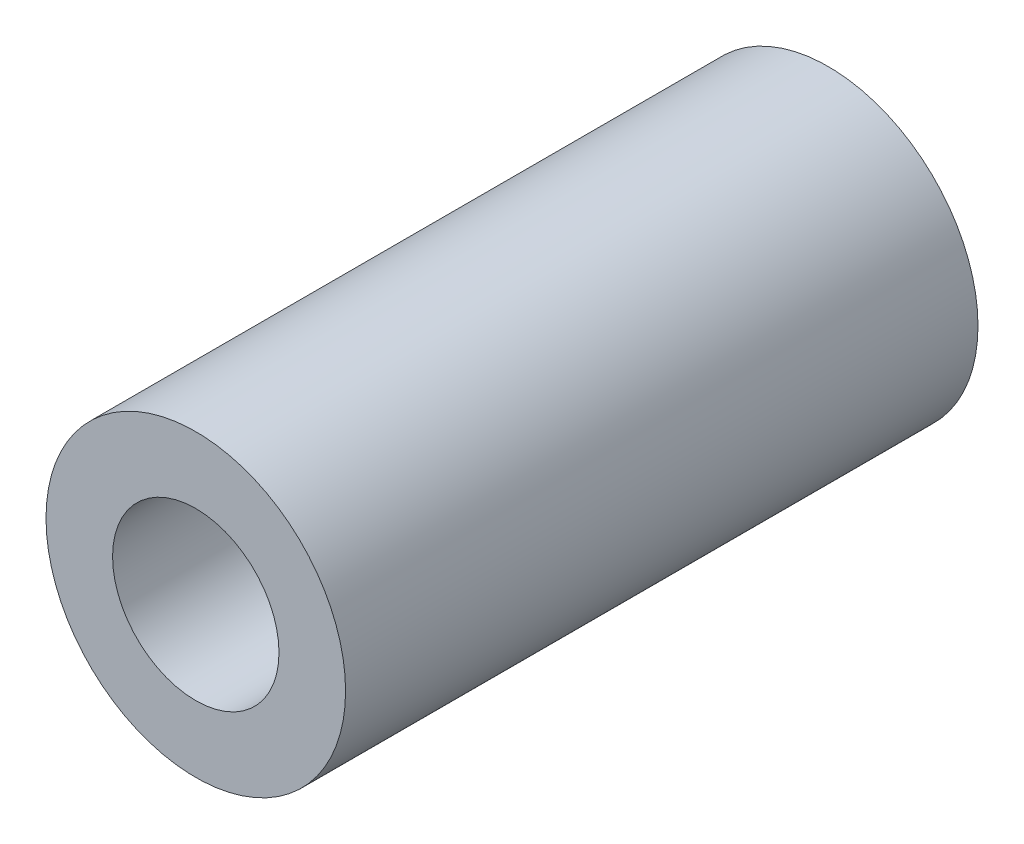
SolidWorks part; units mm, degrees
ref_plane "前视基准面" through (0, 0, 0) normal (0, 0, 1) x (1, 0, 0)
ref_plane "上视基准面" through (0, 0, 0) normal (0, 1, 0) x (1, 0, 0)
ref_plane "右视基准面" through (0, 0, 0) normal (1, 0, 0) x (0, 0, -1)
sketch "Sketch1" plane through (0, 0, 0) normal (0, 0, 1) x (1, 0, 0)
  circle A0 centre (0, 0) radius 2.5
  circle A1 centre (0, 0) radius 4.5
  dimension "D1" = 5
  dimension "D2" = 9
extrude "Boss-Extrude1" add sketch "Sketch1" along normal blind 19
